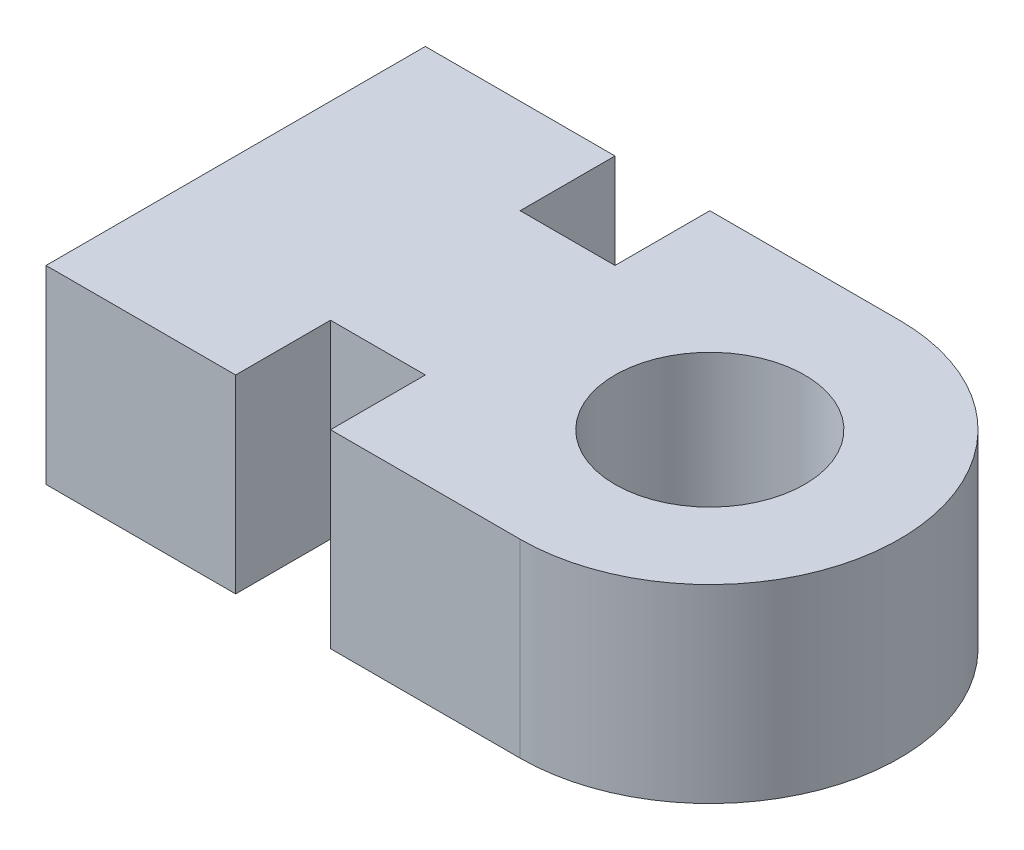
SolidWorks part; units mm, degrees
ref_plane "前基準面" through (0, 0, 0) normal (0, 0, 1) x (1, 0, 0)
ref_plane "上基準面" through (0, 0, 0) normal (0, 1, 0) x (1, 0, 0)
ref_plane "右基準面" through (0, 0, 0) normal (1, 0, 0) x (0, 0, -1)
sketch "草圖1" plane through (0, 0, 0) normal (0, 1, 0) x (1, 0, 0)
  line L0 (0, 0) -> (-16.7995, 0) construction
  line L1 (0, 10) -> (-25, 10)
  line L3 (0, -10) -> (-25, -10)
  line L4 (-25, 10) -> (-25, -10)
  line L5 (-15, 10) -> (-10, 10)
  line L6 (-15, 10) -> (-15, 5)
  line L7 (-15, 5) -> (-10, 5)
  line L8 (-10, 10) -> (-10, 5)
  line L9 (-10, -10) -> (-10, -5)
  line L10 (-15, -10) -> (-15, -5)
  line L11 (-15, -5) -> (-10, -5)
  line L12 (-10, -10) -> (-15, -10)
  circle A0 centre (0, 0) radius 5
  arc A1 (0, -10) -> (0, 10) centre (0, 0) ccw
  dimension "D1" = 20
  dimension "D2" = 10
  dimension "D4" = 5
  dimension "D3" = 25
  dimension "D5" = 5
  dimension "D6" = 10
extrude "填料-伸長1" add sketch "草圖1" along normal blind 10
